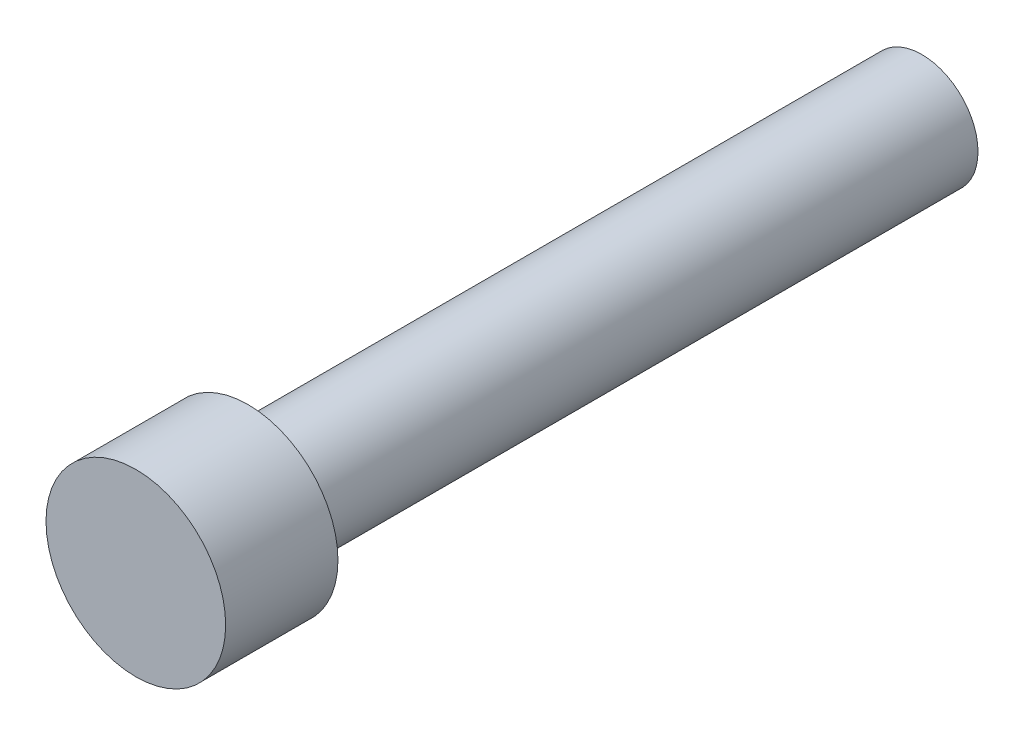
SolidWorks part; units mm, degrees
material "Plain Carbon Steel"
ref_plane "Front Plane" through (0, 0, 0) normal (0, 0, 1) x (1, 0, 0)
ref_plane "Top Plane" through (0, 0, 0) normal (0, 1, 0) x (1, 0, 0)
ref_plane "Right Plane" through (0, 0, 0) normal (1, 0, 0) x (0, 0, -1)
sketch "Sketch1" plane through (0, 0, 0) normal (0, 0, 1) x (1, 0, 0)
  circle A0 centre (0, 0) radius 2.5
  dimension "D1" = 5
extrude "Boss-Extrude1" add sketch "Sketch1" along normal blind 30
sketch "Sketch2" plane through (0, 0, 30) normal (0, 0, 1) x (1, 0, 0)
  circle A0 centre (0, 0) radius 4
  dimension "D1" = 8
extrude "Boss-Extrude2" add sketch "Sketch2" along normal blind 5
